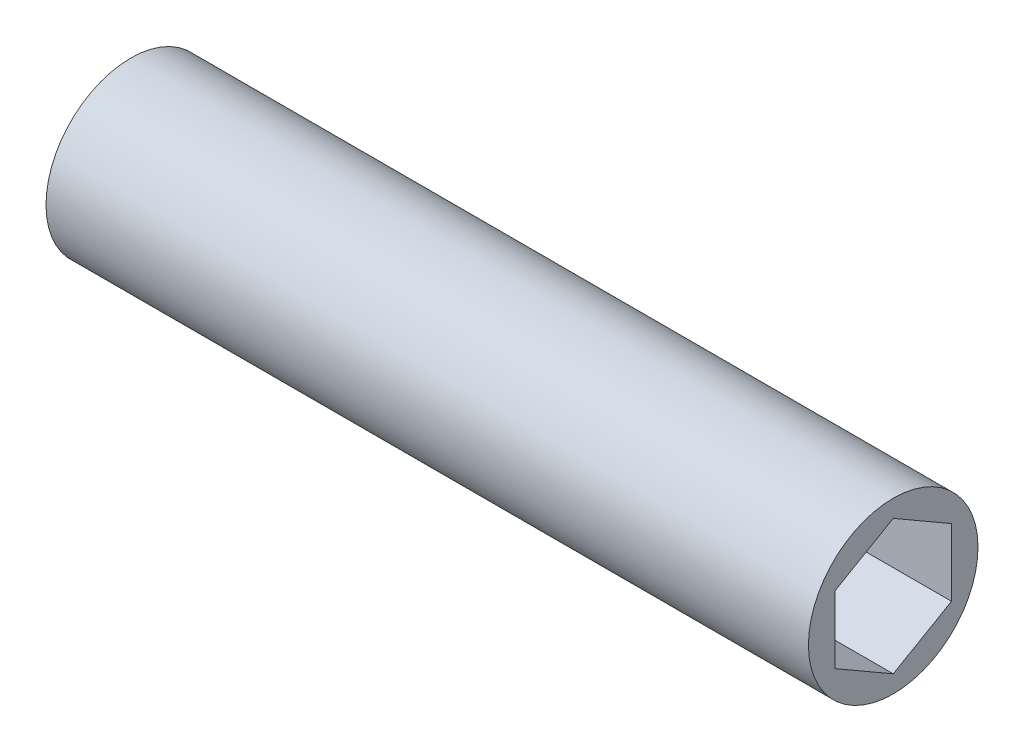
SolidWorks part; units mm, degrees
material "ABS"
ref_plane "Front Plane" through (0, 0, 0) normal (0, 0, 1) x (1, 0, 0)
ref_plane "Top Plane" through (0, 0, 0) normal (0, 1, 0) x (1, 0, 0)
ref_plane "Right Plane" through (0, 0, 0) normal (1, 0, 0) x (0, 0, -1)
sketch "Sketch1" plane through (0, 0, 0) normal (1, 0, 0) x (0, 0, -1)
  line L1 (0, 7.5615) -> (-6.5484, 3.7807)
  line L2 (-6.5484, 3.7807) -> (-6.5484, -3.7807)
  line L3 (-6.5484, -3.7807) -> (0, -7.5615)
  line L4 (0, -7.5615) -> (6.5484, -3.7807)
  line L5 (6.5484, -3.7807) -> (6.5484, 3.7807)
  line L6 (6.5484, 3.7807) -> (0, 7.5615)
  circle A0 centre (0, 0) radius 6.5484 construction
  circle A1 centre (0, 0) radius 9.525
  dimension "D1" = 13.0969
  dimension "D2" = 19.05
extrude "Boss-Extrude1" add sketch "Sketch1" along normal blind 85.6615
